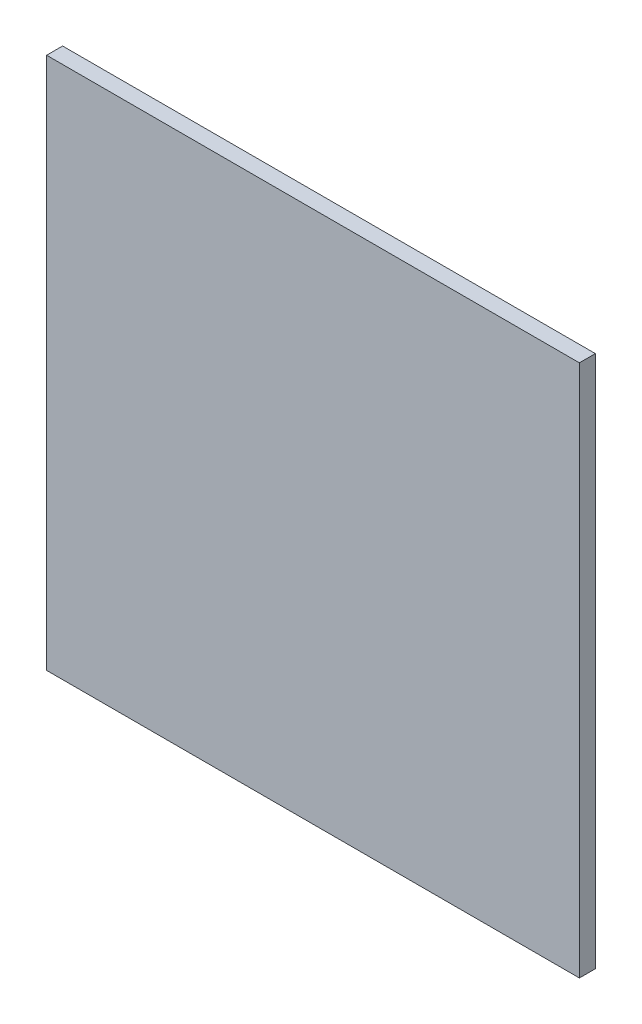
SolidWorks part; units mm, degrees
ref_plane "Alzado" through (0, 0, 0) normal (0, 0, 1) x (1, 0, 0)
ref_plane "Planta" through (0, 0, 0) normal (0, 1, 0) x (1, 0, 0)
ref_plane "Vista lateral" through (0, 0, 0) normal (1, 0, 0) x (0, 0, -1)
sketch "Croquis1" plane through (0, 0, 0) normal (0, 0, 1) x (1, 0, 0)
  line L1 (0, 0) -> (100, 0)
  line L2 (0, 0) -> (0, -100)
  line L3 (0, -100) -> (100, -100)
  line L4 (100, 0) -> (100, -100)
  dimension "D1" = 100
extrude "Saliente-Extruir1" add sketch "Croquis1" along normal blind 3
